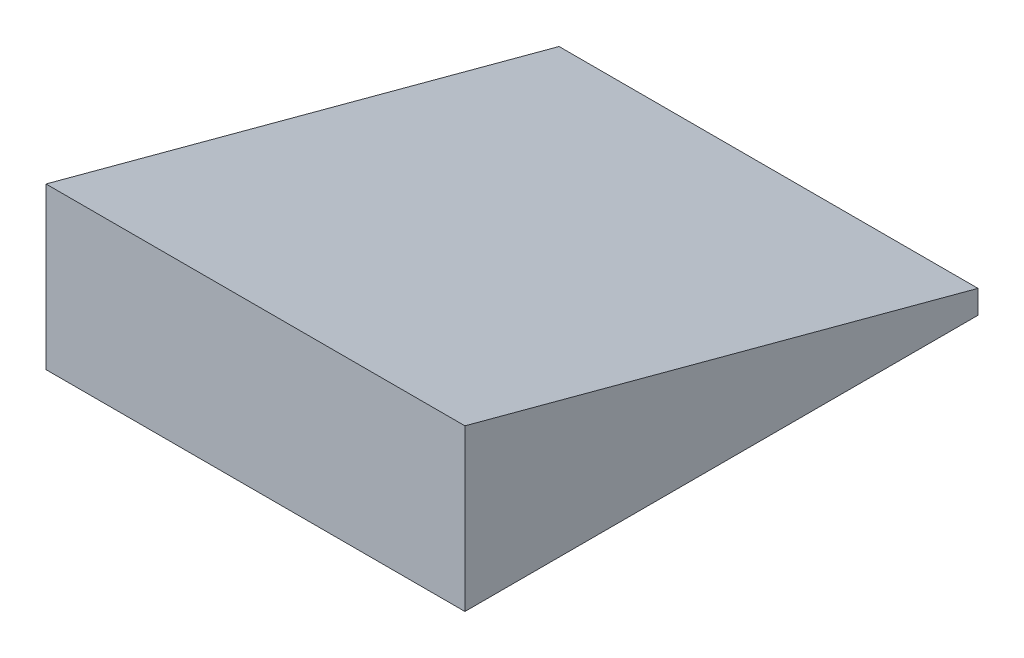
SolidWorks part; units mm, degrees
ref_plane "Спереди" through (0, 0, 0) normal (0, 0, 1) x (1, 0, 0)
ref_plane "Сверху" through (0, 0, 0) normal (0, 1, 0) x (1, 0, 0)
ref_plane "Справа" through (0, 0, 0) normal (1, 0, 0) x (0, 0, -1)
sketch "Эскиз1" plane through (0, 0, 0) normal (0, 1, 0) x (1, 0, 0)
  line L1 (4.102, -15.8696) -> (-175.528, -15.8696)
  line L2 (4.102, -15.8696) -> (4.102, 204.1304)
  line L3 (4.102, 204.1304) -> (-175.528, 204.1304)
  line L4 (-175.528, -15.8696) -> (-175.528, 204.1304)
  dimension "D1" = 220
  dimension "D2" = 179.63
extrude "Бобышка-Вытянуть1" add sketch "Эскиз1" along normal blind 5
sketch "Эскиз2" plane through (0, 5, 0) normal (0, 1, 0) x (1, 0, 0)
  line L1 (4.102, -15.8696) -> (-175.528, -15.8696)
  line L2 (4.102, -15.8696) -> (4.102, 204.1304)
  line L3 (4.102, 204.1304) -> (-175.528, 204.1304)
  line L4 (-175.528, -15.8696) -> (-175.528, 204.1304)
  line L5 (-175.528, 204.1304) -> (-175.528, -15.8696) construction
  dimension "D1" = 220
  dimension "D2" = 179.63
extrude "Бобышка-Вытянуть2" add sketch "Эскиз2" along normal blind 103
sketch "Эскиз3" plane through (4.102, 0, 0) normal (1, 0, 0) x (0, 0, -1)
  line L0 (204.1304, 0) -> (204.1304, 10)
  line L1 (204.1304, 108) -> (204.1304, 0) construction
  line L2 (204.1304, 10) -> (-15.8696, 10)
  line L3 (-15.8696, 108) -> (-15.8696, 0) construction
  line L4 (204.1304, 10) -> (-5.7893, 66.2478)
  line L5 (-5.7893, 66.2478) -> (-22.9942, 70.8579)
  line M3 (204.1304, 0) -> (204.1304, 108)
  line M4 (204.1304, 108) -> (-15.8696, 108)
  line M5 (-15.8696, 108) -> (-15.8696, 0)
  dimension "D1" = 15
extrude "Вырез-Вытянуть1" cut sketch "Эскиз3" against normal blind 375 contours L5 L4 M3 M4 M5
